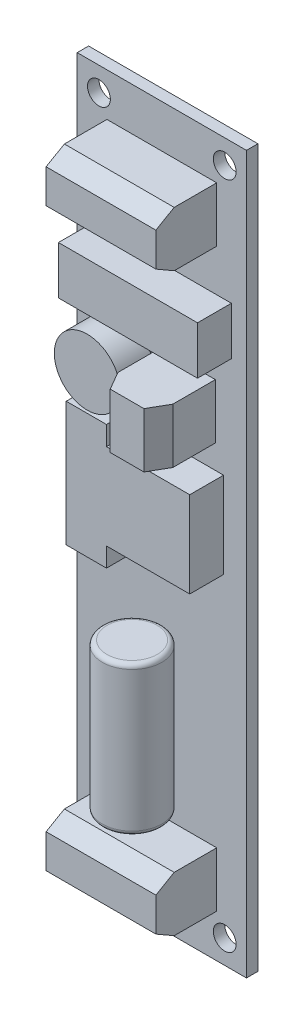
SolidWorks part; units mm, degrees
ref_plane "Front Plane" through (0, 0, 0) normal (0, 0, 1) x (1, 0, 0)
ref_plane "Top Plane" through (0, 0, 0) normal (0, 1, 0) x (1, 0, 0)
ref_plane "Right Plane" through (0, 0, 0) normal (1, 0, 0) x (0, 0, -1)
sketch "Sketch1" plane through (0, 0, 0) normal (0, 0, 1) x (1, 0, 0)
  line L1 (0, 0) -> (23.5, 0)
  line L2 (0, 0) -> (0, -99.5)
  line L3 (0, -99.5) -> (23.5, -99.5)
  line L4 (23.5, 0) -> (23.5, -99.5)
  dimension "D1" = 99.5
  dimension "D2" = 23.5
extrude "Boss-Extrude1" add sketch "Sketch1" along normal blind 1.5875
sketch "Sketch2" plane through (0, 0, 0) normal (0, 0, -1) x (-1, 0, 0)
  line L0 (-11.75, 0) -> (-11.75, -99.5) construction
  line L1 (-23.5, 0) -> (0, 0) construction
  line L2 (0, -99.5) -> (-23.5, -99.5) construction
  line L3 (-23.5, -49.75) -> (0, -49.75) construction
  line L4 (-23.5, -99.5) -> (-23.5, 0) construction
  line L5 (0, 0) -> (0, -99.5) construction
  circle A0 centre (-20.4813, -3.3156) radius 1.5875
  circle A1 centre (-3.0188, -3.3156) radius 1.5875
  circle A2 centre (-3.0188, -96.1844) radius 1.5875
  circle A3 centre (-20.4813, -96.1844) radius 1.5875
  dimension "D1" = 3.175
  dimension "D2" = 92.8688
  dimension "D3" = 17.4625
extrude "Cut-Extrude1" cut sketch "Sketch2" against normal through all
sketch "Sketch5" plane through (0, 0, 1.5875) normal (0, 0, 1) x (1, 0, 0)
  line L0 (11.75, 0) -> (11.75, -99.5) construction
  line L1 (4.13, -5.969) -> (19.37, -5.969)
  line L2 (4.13, -5.969) -> (4.13, -13.589)
  line L3 (4.13, -13.589) -> (19.37, -13.589)
  line L4 (19.37, -5.969) -> (19.37, -13.589)
  line L5 (11.562, -29.718) -> (19.182, -29.718)
  line L6 (11.562, -29.718) -> (11.562, -37.338)
  line L7 (11.562, -37.338) -> (19.182, -37.338)
  line L8 (19.182, -29.718) -> (19.182, -37.338)
  line L13 (23.5, 0) -> (0, 0) construction
  line L14 (0, -99.5) -> (23.5, -99.5) construction
  line L15 (0, 0) -> (0, -99.5) construction
  line L22 (0, -49.75) -> (23.5, -49.75) construction
  line L23 (23.5, -99.5) -> (23.5, 0) construction
  line L24 (19.37, -93.531) -> (19.37, -85.911)
  line L25 (4.13, -85.911) -> (19.37, -85.911)
  line L26 (4.13, -93.531) -> (4.13, -85.911)
  line L27 (4.13, -93.531) -> (19.37, -93.531)
  point P19 (11.75, -5.969)
  dimension "D1" = 15.24
  dimension "D2" = 7.62
  dimension "D3" = 5.969
  dimension "D4" = 7.62
  dimension "D5" = 7.62
  dimension "D6" = 4.318
  dimension "D7" = 29.718
extrude "Boss-Extrude2" add sketch "Sketch5" along normal blind 8.4455
chamfer "Chamfer1" distance 2.54 angle 30 6 edges at (11.75, -93.531, 10.033) (11.75, -85.911, 10.033) (19.182, -33.528, 10.033) (11.562, -33.528, 10.033) (11.75, -13.589, 10.033) (11.75, -5.969, 10.033)
ref_plane "Plane1" through (0, -83.371, 0) normal (0, 1, 0) x (1, 0, 0)
sketch "Sketch6" plane through (0, -83.371, 0) normal (0, 1, 0) x (1, 0, 0)
  line L0 (19.37, -1.5875) -> (4.13, -1.5875) construction
  line L1 (11.75, -1.5875) -> (11.75, -5.715) construction
  circle A0 centre (11.75, -5.715) radius 4.1275
  point P4 (11.75, -1.5875)
  dimension "D1" = 8.255
extrude "Boss-Extrude3" add sketch "Sketch6" along normal blind 20.701 separate body
fillet "Fillet1" radius 0.635 2 edges at (11.75, -83.371, 9.8425) (11.75, -62.67, 9.8425)
sketch "Sketch7" plane through (0, 0, 1.5875) normal (0, 0, 1) x (1, 0, 0)
  line L0 (11.75, 0) -> (11.75, -99.5) construction
  line L1 (23.5, 0) -> (0, 0) construction
  line L2 (0, -99.5) -> (23.5, -99.5) construction
  line L3 (0, 0) -> (0, -99.5) construction
  line L4 (2.098, -19.431) -> (21.402, -19.431)
  line L5 (2.098, -19.431) -> (2.098, -26.0985)
  line L6 (2.098, -26.0985) -> (21.402, -26.0985)
  line L7 (21.402, -19.431) -> (21.402, -26.0985)
  line L8 (8.7655, -52.578) -> (8.7655, -55.245)
  line L9 (8.7655, -40.64) -> (20.3225, -40.64)
  line L11 (8.7655, -52.578) -> (20.3225, -52.578)
  line L12 (20.3225, -40.64) -> (20.3225, -52.578)
  line L13 (3.1775, -37.973) -> (8.7655, -37.973)
  line L14 (3.1775, -37.973) -> (3.1775, -55.245)
  line L15 (3.1775, -55.245) -> (8.7655, -55.245)
  line L16 (8.7655, -37.973) -> (8.7655, -40.64)
  line L17 (3.1775, -46.609) -> (20.3225, -46.609) construction
  circle A0 centre (6.096, -33.02) radius 4.572
  point P4 (11.75, -19.431)
  point P23 (11.75, -46.609)
  dimension "D4" = 9.144
  dimension "D1" = 19.304
  dimension "D2" = 6.6675
  dimension "D3" = 19.431
  dimension "D5" = 6.096
  dimension "D6" = 17.145
  dimension "D7" = 33.02
  dimension "D8" = 17.272
  dimension "D9" = 11.938
  dimension "D10" = 5.588
  dimension "D11" = 40.64
extrude "Boss-Extrude4" add sketch "Sketch7" along normal blind 4.699
